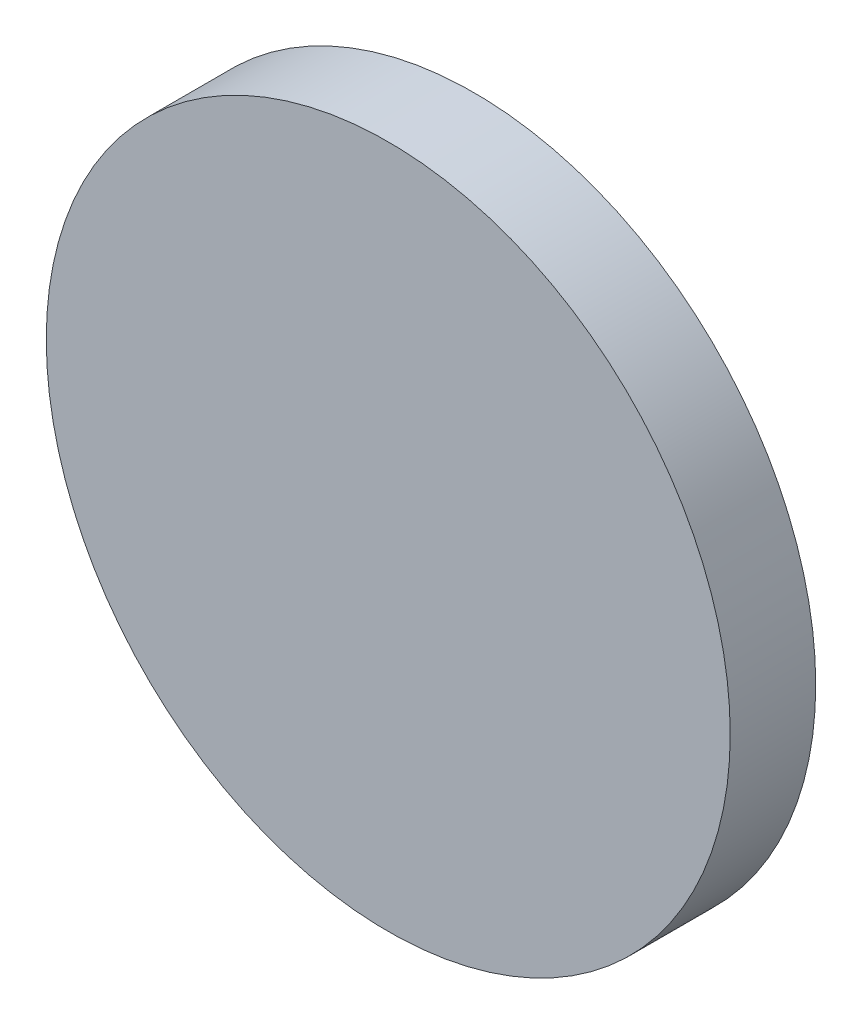
SolidWorks part; units mm, degrees
ref_plane "Front Plane" through (0, 0, 0) normal (0, 0, 1) x (1, 0, 0)
ref_plane "Top Plane" through (0, 0, 0) normal (0, 1, 0) x (1, 0, 0)
ref_plane "Right Plane" through (0, 0, 0) normal (1, 0, 0) x (0, 0, -1)
sketch "Sketch1" plane through (0, 0, 0) normal (0, 0, 1) x (1, 0, 0)
  circle A0 centre (0, 0) radius 20
  dimension "D1" = 40
extrude "Boss-Extrude1" add sketch "Sketch1" against normal blind 5
